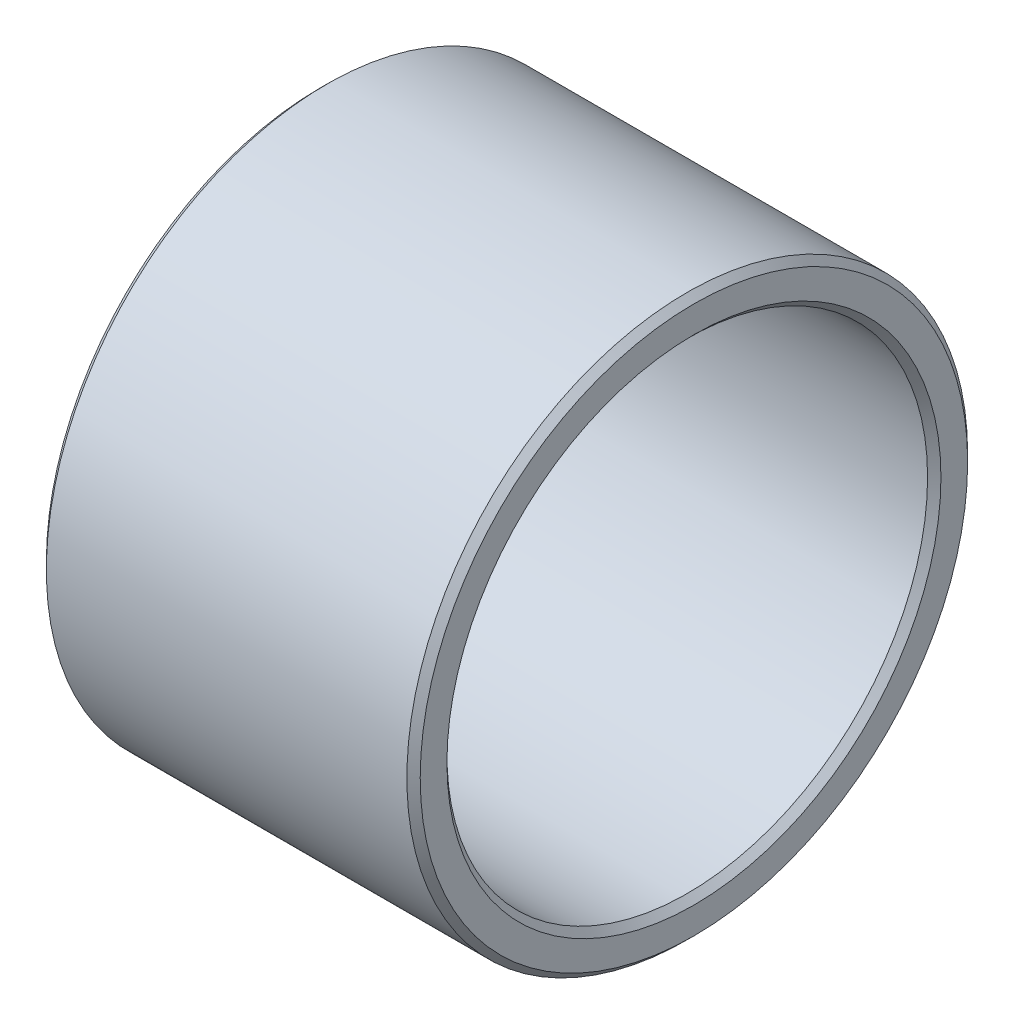
SolidWorks part; units mm, degrees
material "普通碳钢"
ref_plane "Front" through (0, 0, 0) normal (0, 0, 1) x (1, 0, 0)
ref_plane "Top" through (0, 0, 0) normal (0, 1, 0) x (1, 0, 0)
ref_plane "Right" through (0, 0, 0) normal (1, 0, 0) x (0, 0, -1)
sketch "草图1" plane through (0, 0, 0) normal (1, 0, 0) x (0, 0, -1)
  circle A0 centre (0, 0) radius 18
  circle A1 centre (0, 0) radius 21
  dimension "D1" = 36
  dimension "D2" = 3
extrude "凸台-拉伸1" add sketch "草图1" along normal blind 28
chamfer "倒角1" distance 0.5 angle 45 4 edges at (0, 0, -18) (0, 0, -21) (28, 0, -18) (28, 0, -21)
